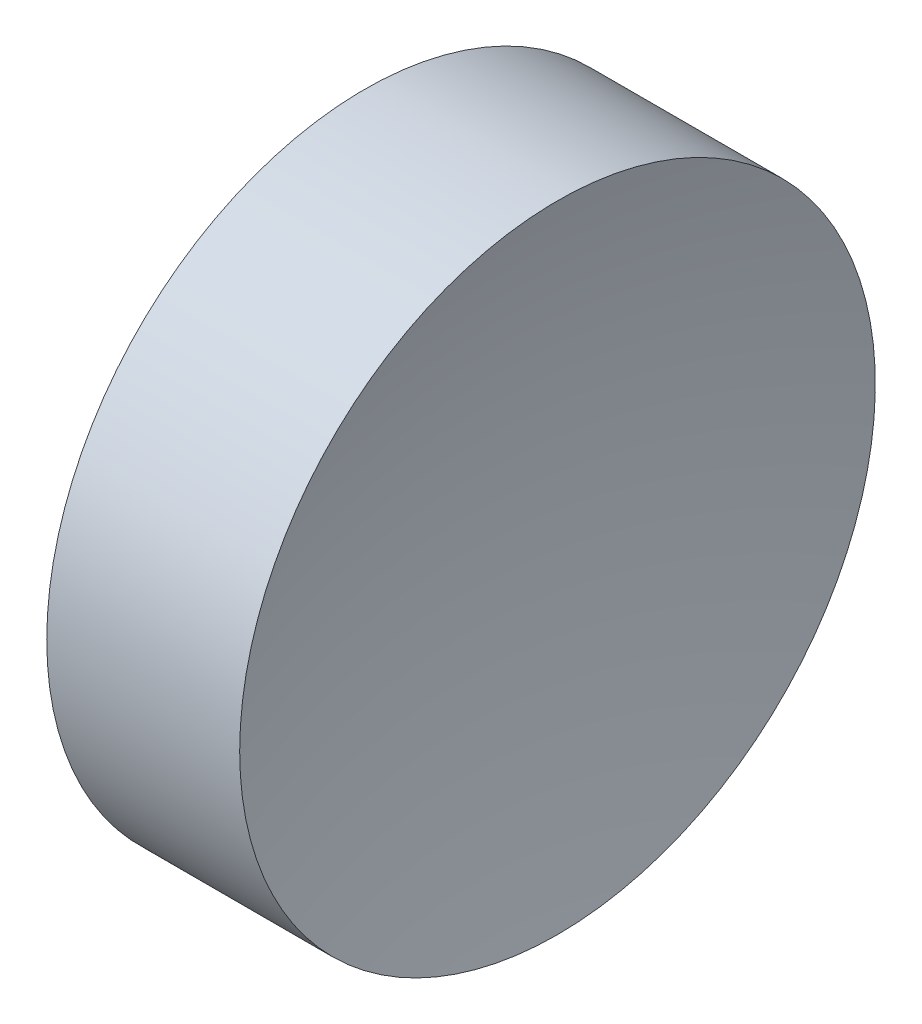
SolidWorks part; units mm, degrees
ref_plane "前视基准面" through (0, 0, 0) normal (0, 0, 1) x (1, 0, 0)
ref_plane "上视基准面" through (0, 0, 0) normal (0, 1, 0) x (1, 0, 0)
ref_plane "右视基准面" through (0, 0, 0) normal (1, 0, 0) x (0, 0, -1)
sketch "草图1" plane through (0, 0, 0) normal (0, 0, 1) x (1, 0, 0)
  line L0 (108.9851, 69.378) -> (132.7763, 69.378) construction
  line L1 (115.0927, 69.378) -> (115.0927, 81.878)
  line L2 (115.0927, 81.878) -> (122.6804, 81.878)
  line L3 (121.0927, 69.378) -> (115.0927, 69.378)
  arc A0 (122.6804, 81.878) -> (121.0927, 69.378) centre (171.0927, 69.378) ccw
revolve "旋转1" add sketch "草图1" angle 360 about L0
